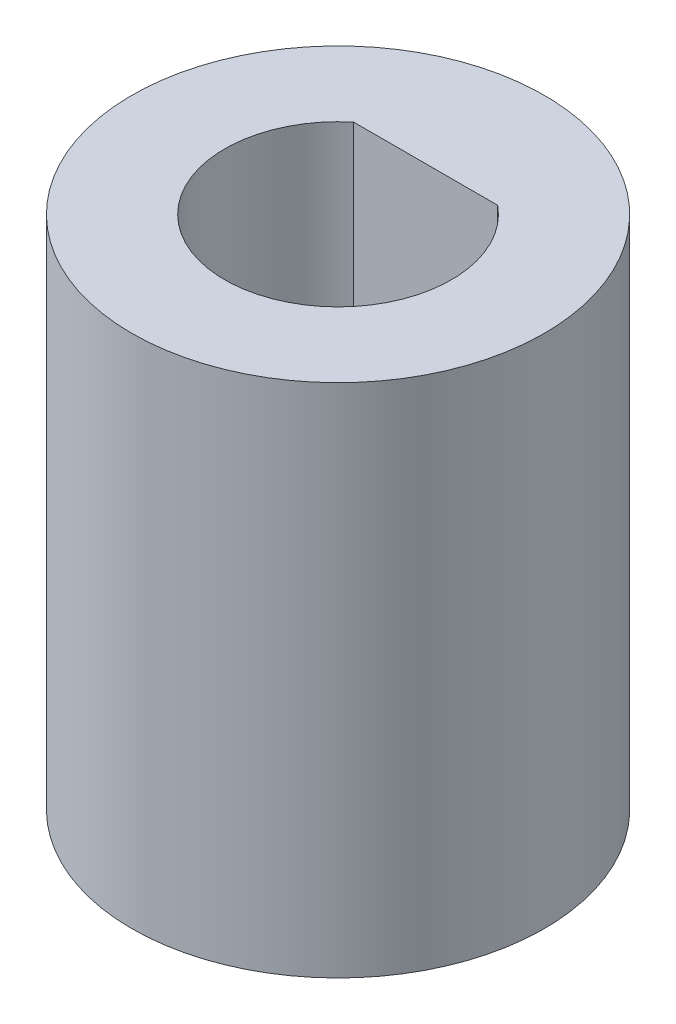
SolidWorks part; units mm, degrees
ref_plane "Front Plane" through (0, 0, 0) normal (0, 0, 1) x (1, 0, 0)
ref_plane "Top Plane" through (0, 0, 0) normal (0, 1, 0) x (1, 0, 0)
ref_plane "Right Plane" through (0, 0, 0) normal (1, 0, 0) x (0, 0, -1)
sketch "Sketch1" plane through (0, 0, 0) normal (0, 1, 0) x (1, 0, 0)
  line L0 (-1.3964, 1.7) -> (1.3964, 1.7)
  circle A0 centre (0, 0) radius 4
  circle A1 centre (0, 0) radius 2.2
  dimension "D1" = 8
  dimension "D2" = 4.4
  dimension "D3" = 0.5
extrude "Boss-Extrude1" add sketch "Sketch1" along normal blind 10 contours A0 A1 | L0 A1
